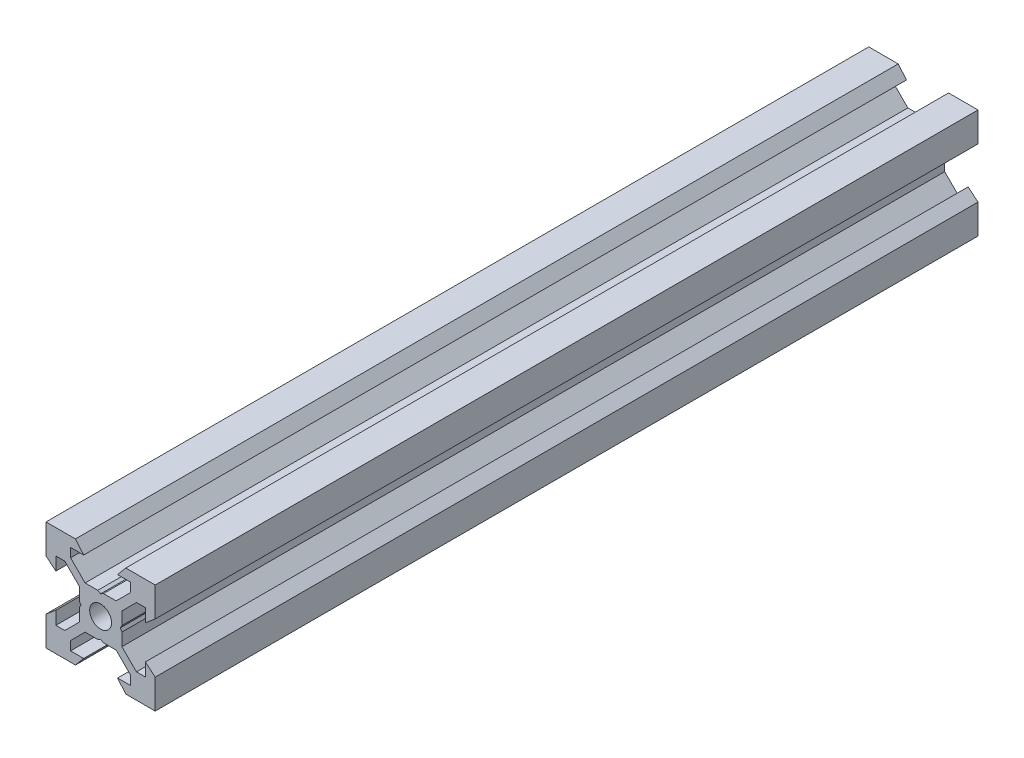
SolidWorks part; units mm, degrees
ref_plane "Front Plane" through (0, 0, 0) normal (0, 0, 1) x (1, 0, 0)
ref_plane "Top Plane" through (0, 0, 0) normal (0, 1, 0) x (1, 0, 0)
ref_plane "Right Plane" through (0, 0, 0) normal (1, 0, 0) x (0, 0, -1)
sketch "Sketch1" plane through (0, 0, 0) normal (0, 0, 1) x (1, 0, 0)
  line L0 (10, 10) -> (4.6104, 10) construction
  line L1 (10, 10) -> (10, 4.6104) construction
  line L2 (10, -10) -> (10, -4.6104) construction
  line L3 (10, -10) -> (4.6104, -10) construction
  line L4 (10, 10) -> (10, 4.6104)
  line L5 (6.5607, 5.5) -> (8.2, 5.5)
  line L6 (5.5, 8.2) -> (5.5, 6.5607)
  line L7 (10, 10) -> (4.6104, 10)
  line L8 (10, 10) -> (10, 4.6104)
  line L9 (6.5607, 5.5) -> (3.9, 2.8393)
  line L10 (5.5, 6.5607) -> (2.8393, 3.9)
  line L11 (10, 4.6104) -> (8.2, 3.1)
  line L12 (4.6104, 10) -> (3.1, 8.2)
  line L13 (8.2, 3.1) -> (8.2, 5.5)
  line L14 (3.1, 8.2) -> (5.5, 8.2)
  line L15 (-6.5607, 5.5) -> (-8.2, 5.5)
  line L16 (6.5607, -5.5) -> (8.2, -5.5)
  line L17 (3.1, -8.2) -> (5.5, -8.2)
  line L18 (8.2, -3.1) -> (8.2, -5.5)
  line L19 (4.6104, -10) -> (3.1, -8.2)
  line L20 (10, -4.6104) -> (8.2, -3.1)
  line L21 (0.5196, -3.9) -> (0, -3.6)
  line L22 (0.5196, 3.9) -> (0, 3.6)
  line L23 (3.6, 0) -> (3.9, -0.5196)
  line L24 (3.9, 0.5196) -> (3.6, 0)
  line L25 (3.9, 0.5196) -> (3.9, 2.8393)
  line L26 (2.8393, 3.9) -> (0.5196, 3.9)
  line L27 (3.9, -2.8393) -> (3.9, -0.5196)
  line L28 (2.8393, -3.9) -> (0.5196, -3.9)
  line L29 (5.5, -6.5607) -> (2.8393, -3.9)
  line L30 (6.5607, -5.5) -> (3.9, -2.8393)
  line L31 (10, -10) -> (10, -4.6104)
  line L32 (10, -10) -> (4.6104, -10)
  line L33 (5.5, -8.2) -> (5.5, -6.5607)
  line L34 (-6.5607, -5.5) -> (-8.2, -5.5)
  line L35 (10, -10) -> (10, -4.6104)
  line L36 (0, 0) -> (0, 8.2) construction
  line L37 (-10, -10) -> (-4.6104, -10) construction
  line L38 (-10, -10) -> (-10, -4.6104) construction
  line L39 (-10, 10) -> (-10, 4.6104) construction
  line L40 (-10, 10) -> (-4.6104, 10) construction
  line L41 (-10, -10) -> (-10, -4.6104)
  line L43 (-5.5, -8.2) -> (-5.5, -6.5607)
  line L44 (-10, -10) -> (-4.6104, -10)
  line L45 (-10, -10) -> (-10, -4.6104)
  line L46 (-6.5607, -5.5) -> (-3.9, -2.8393)
  line L47 (-5.5, -6.5607) -> (-2.8393, -3.9)
  line L48 (-2.8393, -3.9) -> (-0.5196, -3.9)
  line L49 (-3.9, -2.8393) -> (-3.9, -0.5196)
  line L50 (-2.8393, 3.9) -> (-0.5196, 3.9)
  line L51 (-3.9, 0.5196) -> (-3.9, 2.8393)
  line L52 (-3.9, 0.5196) -> (-3.6, 0)
  line L53 (-3.6, 0) -> (-3.9, -0.5196)
  line L54 (-0.5196, 3.9) -> (0, 3.6)
  line L55 (-0.5196, -3.9) -> (0, -3.6)
  line L56 (-10, -4.6104) -> (-8.2, -3.1)
  line L57 (-4.6104, -10) -> (-3.1, -8.2)
  line L58 (-8.2, -3.1) -> (-8.2, -5.5)
  line L59 (-3.1, -8.2) -> (-5.5, -8.2)
  line L60 (-10, -10) -> (10, -10) construction
  line L61 (-10, -10) -> (-10, 10) construction
  line L62 (-3.1, 8.2) -> (-5.5, 8.2)
  line L63 (-8.2, 3.1) -> (-8.2, 5.5)
  line L64 (-4.6104, 10) -> (-3.1, 8.2)
  line L65 (-10, 4.6104) -> (-8.2, 3.1)
  line L66 (-5.5, 6.5607) -> (-2.8393, 3.9)
  line L67 (-6.5607, 5.5) -> (-3.9, 2.8393)
  line L68 (-10, 10) -> (-10, 4.6104)
  line L69 (-10, 10) -> (-4.6104, 10)
  line L70 (-5.5, 8.2) -> (-5.5, 6.5607)
  line L71 (-10, 10) -> (10, 10) construction
  line L72 (-10, 10) -> (-10, 4.6104)
  line L73 (10, -10) -> (10, 10) construction
  line L74 (-10, -10) -> (10, 10) construction
  line L75 (-10, 10) -> (10, -10) construction
  circle A0 centre (0, 0) radius 2
  dimension "D7" = 4
  dimension "D1" = 20
  dimension "D2" = 5.3896
  dimension "D3" = 4.5
  dimension "D4" = 50
  dimension "D5" = 1.8
  dimension "D6" = 1.5104
  dimension "D8" = 5.5
  dimension "D9" = 120
  dimension "D10" = 0.3
  dimension "D11" = 2.3197
  dimension "D12" = 7.8
  dimension "D13" = 7.8
  dimension "D14" = 1.5
  dimension "D15" = 2.6607
extrude "Boss-Extrude1" add sketch "Sketch1" along normal mid plane 150.67 contours L70 L62 L64 L69 L68 L65 L63 L15 L67 L51 L52 L53 L49 L46 L34 L58 L56 L41 L44 L57 L59 L43 L47 L48 L55 L21 L28 L29 L33 L17 L19 L32 L31 L20 L18 L16 L30 L27 L23 L24 L25 L9 L5 L13 L11 L4 L7 L12 L14 L6 L10
